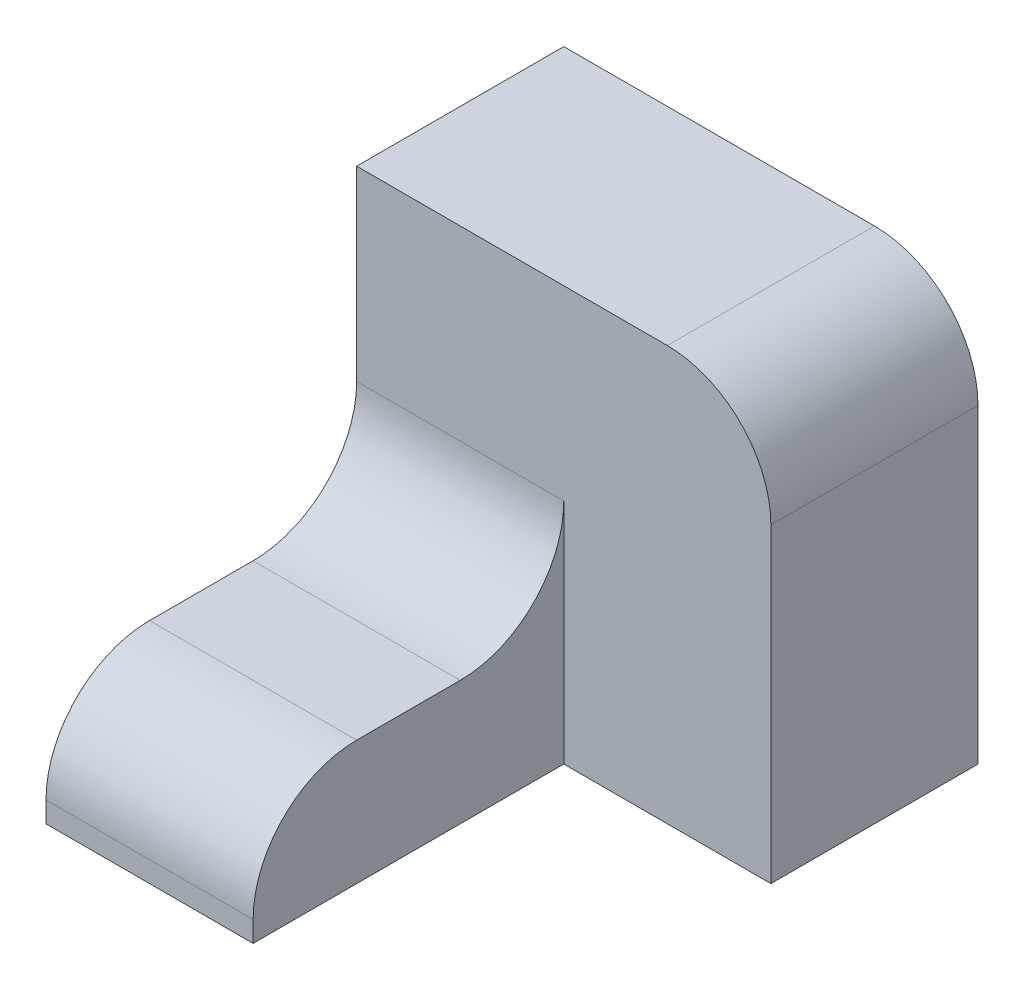
SolidWorks part; units mm, degrees
ref_plane "Front Plane" through (0, 0, 0) normal (0, 0, 1) x (1, 0, 0)
ref_plane "Top Plane" through (0, 0, 0) normal (0, 1, 0) x (1, 0, 0)
ref_plane "Right Plane" through (0, 0, 0) normal (1, 0, 0) x (0, 0, -1)
sketch "Sketch1" plane through (0, 0, 0) normal (0, 0, 1) x (1, 0, 0)
  line L1 (-30, -12) -> (-10, -12)
  line L2 (-10, -12) -> (-10, 0)
  line L3 (-10, 0) -> (-30, 0)
  line L4 (-30, 0) -> (-30, -12)
  dimension "D1" = 20
  dimension "Width" = 12
extrude "Boss-Extrude1" add sketch "Sketch1" along normal blind 30
sketch "Sketch2" plane through (0, 0, 0) normal (0, 0, 1) x (1, 0, 0)
  line L1 (-30, -12) -> (10, -12)
  line L2 (10, -12) -> (10, 28)
  line L3 (10, 28) -> (-30, 28)
  line L4 (-30, 28) -> (-30, -12)
  dimension "D1" = 40
  dimension "Width" = 40
extrude "Boss-Extrude2" add sketch "Sketch2" against normal blind 20
fillet "Fillet1" radius 10 3 edges at (-20, 0, 0) (10, 28, -10) (-20, 0, 30)
